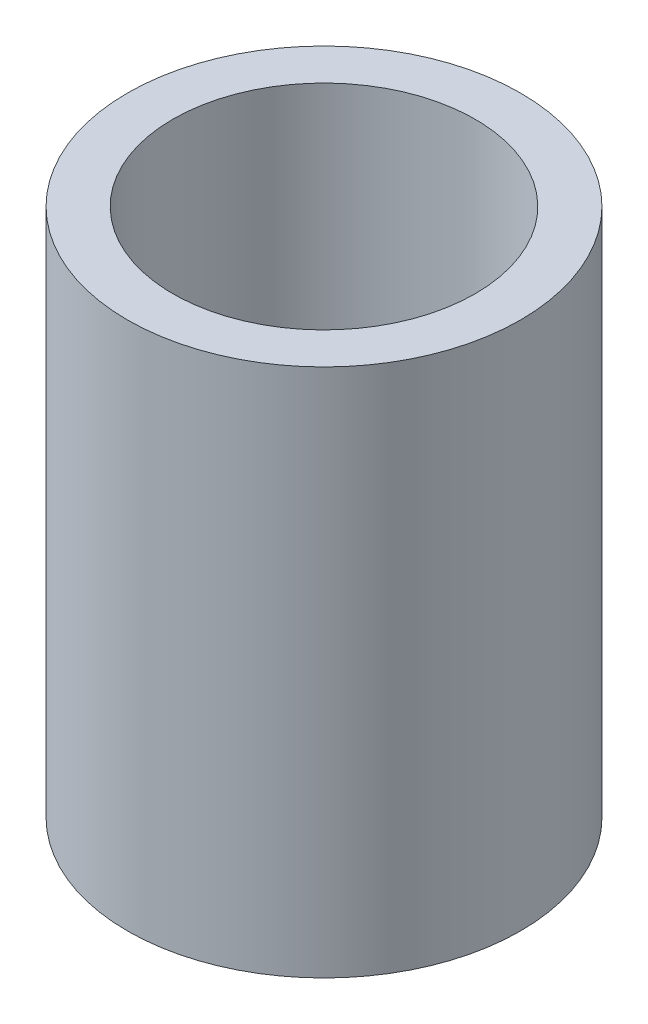
SolidWorks part; units mm, degrees
ref_plane "Front Plane" through (0, 0, 0) normal (0, 0, 1) x (1, 0, 0)
ref_plane "Top Plane" through (0, 0, 0) normal (0, 1, 0) x (1, 0, 0)
ref_plane "Right Plane" through (0, 0, 0) normal (1, 0, 0) x (0, 0, -1)
sketch "Sketch1" plane through (0, 0, 0) normal (0, 1, 0) x (1, 0, 0)
  circle A0 centre (0, 0) radius 23
  dimension "D1" = 46
extrude "Extrude-Thin1" add sketch "Sketch1" along normal blind 70 thin thin type mid plane wall 6
